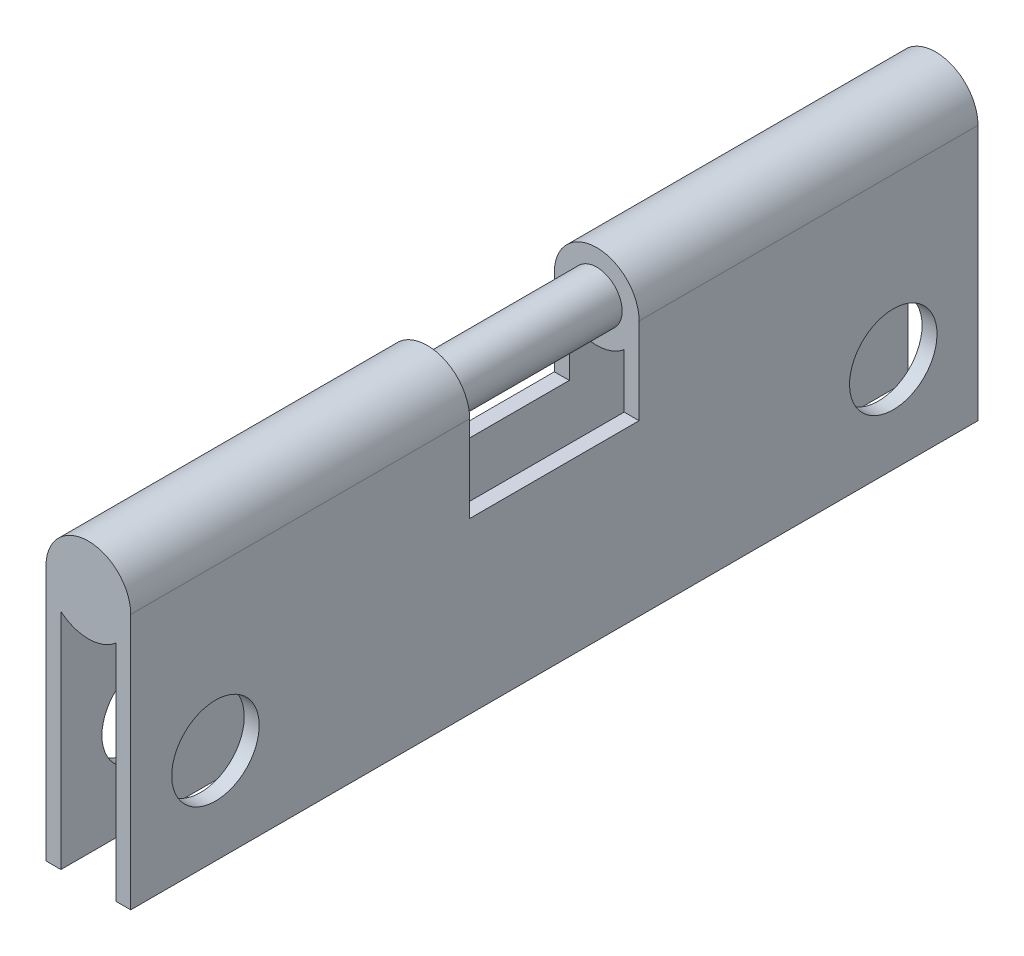
SolidWorks part; units mm, degrees
ref_plane "Front Plane" through (0, 0, 0) normal (0, 0, 1) x (1, 0, 0)
ref_plane "Top Plane" through (0, 0, 0) normal (0, 1, 0) x (1, 0, 0)
ref_plane "Right Plane" through (0, 0, 0) normal (1, 0, 0) x (0, 0, -1)
sketch "Sketch1" plane through (0, 0, 0) normal (0, 0, 1) x (1, 0, 0)
  line L0 (1.5875, 0) -> (1.5875, -9.5885)
  line L1 (1.5875, -9.5885) -> (1.0287, -9.5885)
  line L2 (1.0287, -9.5885) -> (1.0287, -1.2091)
  line L3 (-1.5875, 0) -> (-1.5875, -9.5885)
  line L4 (-1.5875, -9.5885) -> (-1.0287, -9.5885)
  line L5 (-1.0287, -9.5885) -> (-1.0287, -1.2091)
  arc A0 (-1.0287, -1.2091) -> (1.0287, -1.2091) centre (0, 0) ccw
  arc A1 (1.5875, 0) -> (-1.5875, 0) centre (0, 0) ccw
  dimension "D1" = 3.175
  dimension "D2" = 9.5885
  dimension "D3" = 0.5588
extrude "Boss-Extrude1" add sketch "Sketch1" along normal blind 31.75
sketch "Sketch2" plane through (1.5875, 0, 0) normal (1, 0, 0) x (0, 0, -1)
  line L0 (-31.75, -6.0071) -> (0, -6.0071) construction
  line L1 (-31.75, -9.5885) -> (-31.75, 0) construction
  line L2 (0, -9.5885) -> (0, 0) construction
  line L3 (-31.75, -9.5885) -> (0, -9.5885) construction
  line L4 (0, 1.5875) -> (-31.75, 1.5875) construction
  line L5 (-19.05, 1.5875) -> (-12.7, 1.5875)
  line L6 (-19.05, 1.5875) -> (-19.05, -3.2385)
  line L7 (-19.05, -3.2385) -> (-12.7, -3.2385)
  line L8 (-12.7, 1.5875) -> (-12.7, -3.2385)
  line L9 (-19.05, 1.5875) -> (-12.7, -3.2385) construction
  line L10 (-19.05, -3.2385) -> (-12.7, 1.5875) construction
  circle A0 centre (-28.575, -6.0071) radius 1.6383
  circle A1 centre (-3.175, -6.0071) radius 1.6383
  point P16 (-15.875, -0.8255)
  dimension "D1" = 3.2766
  dimension "D2" = 3.175
  dimension "D3" = 25.4
  dimension "D4" = 3.5814
  dimension "D5" = 6.35
  dimension "D6" = 4.826
  dimension "D7" = 12.7
extrude "Cut-Extrude1" cut sketch "Sketch2" against normal through all
sketch "Sketch3" plane through (0, 0, 12.7) normal (0, 0, 1) x (1, 0, 0)
  circle A0 centre (0, 0) radius 0.9525
  dimension "D1" = 1.905
extrude "Boss-Extrude2" add sketch "Sketch3" along normal up to next
equation "\"D7@Sketch2\"=\"D3@Sketch2\"/2"
